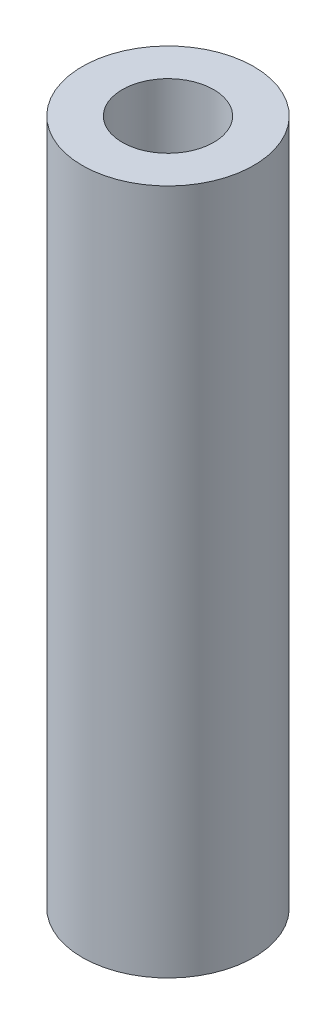
SolidWorks part; units mm, degrees
ref_plane "Front Plane" through (0, 0, 0) normal (0, 0, 1) x (1, 0, 0)
ref_plane "Top Plane" through (0, 0, 0) normal (0, 1, 0) x (1, 0, 0)
ref_plane "Right Plane" through (0, 0, 0) normal (1, 0, 0) x (0, 0, -1)
sketch "Croquis1" plane through (0, 0, 0) normal (1, 0, 0) x (0, 0, -1)
  line L0 (0, 0) -> (0, 98.5333) construction
  line L1 (8, 0) -> (15, 0)
  line L2 (8, 0) -> (8, 120)
  line L3 (8, 120) -> (15, 120)
  line L4 (15, 0) -> (15, 120)
  dimension "D1" = 16
  dimension "D2" = 7
  dimension "D3" = 120
revolve "Revolución1" add sketch "Croquis1" angle 360 about L0
equation "\"OD\"=24.2963"
equation "\"Pared\"=5.13824"
equation "\"Altura\"=66.7971"
